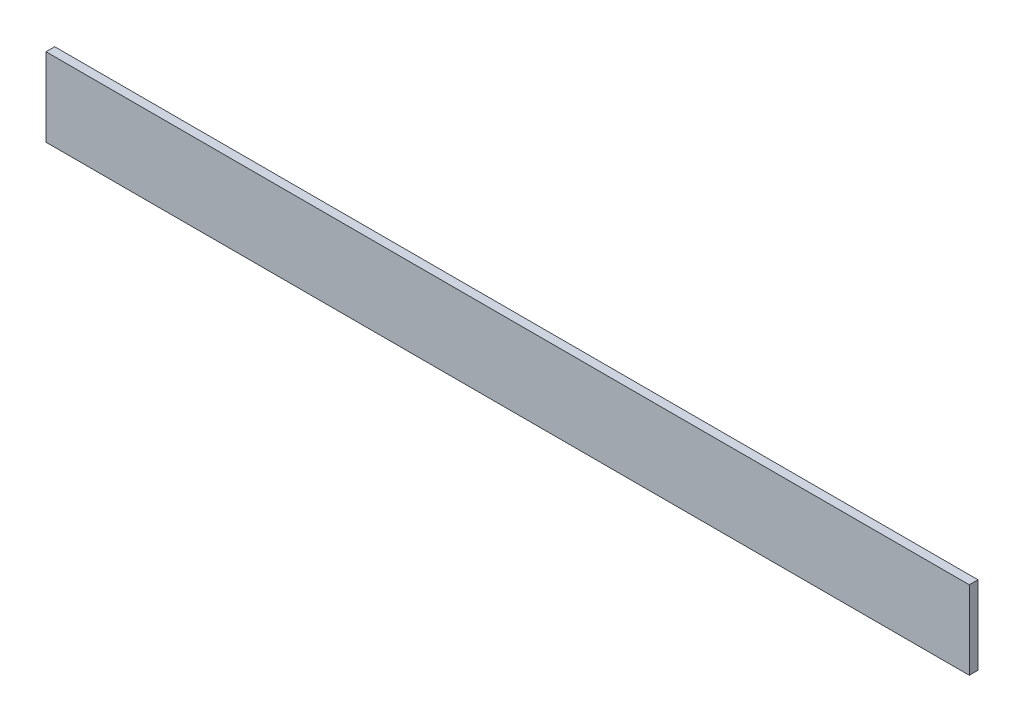
SolidWorks part; units mm, degrees
ref_plane "Front" through (0, 0, 0) normal (0, 0, 1) x (1, 0, 0)
ref_plane "Top" through (0, 0, 0) normal (0, 1, 0) x (1, 0, 0)
ref_plane "Right" through (0, 0, 0) normal (1, 0, 0) x (0, 0, -1)
sketch "Sketch1" plane through (0, 0, 0) normal (0, 0, 1) x (1, 0, 0)
  line L1 (1060, 90) -> (-1060, 90)
  line L2 (1060, 90) -> (1060, -90)
  line L3 (1060, -90) -> (-1060, -90)
  line L4 (-1060, 90) -> (-1060, -90)
  line L5 (1060, 90) -> (-1060, -90) construction
  line L6 (1060, -90) -> (-1060, 90) construction
  point P0 (0, 0)
  dimension "D1" = 2120
  dimension "D2" = 180
extrude "Boss-Extrude1" add sketch "Sketch1" along normal mid plane 20
